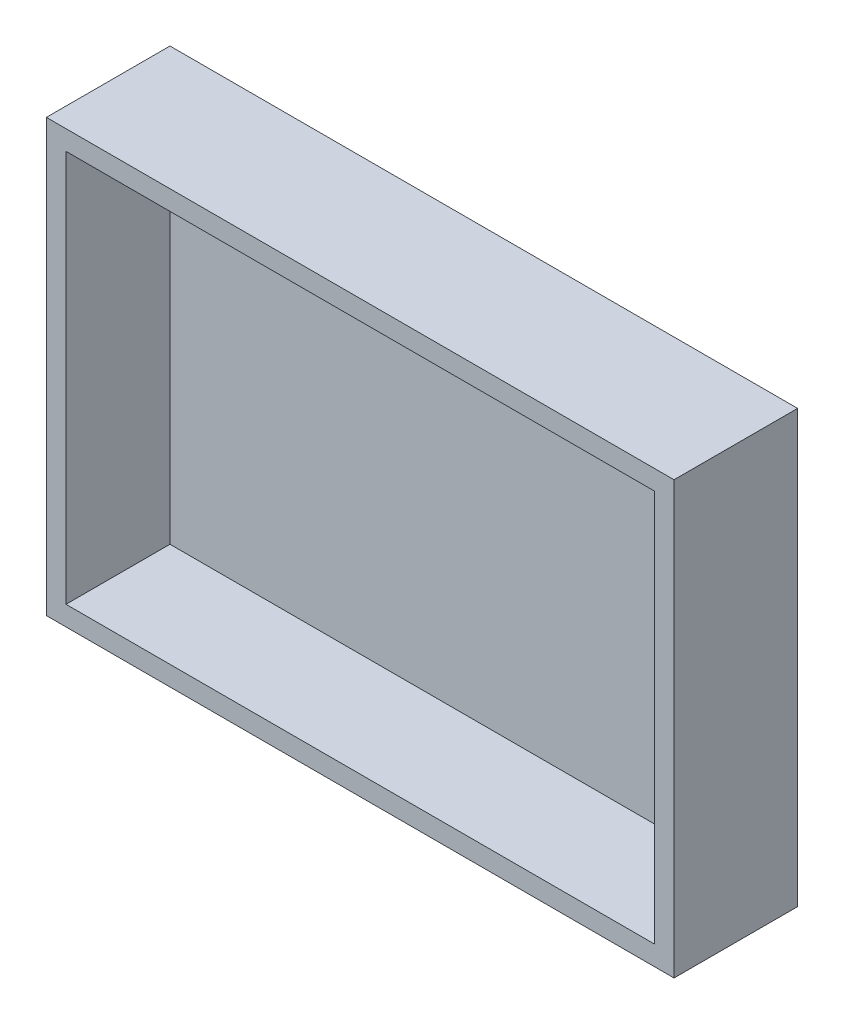
SolidWorks part; units mm, degrees
ref_plane "Front Plane" through (0, 0, 0) normal (0, 0, 1) x (1, 0, 0)
ref_plane "Top Plane" through (0, 0, 0) normal (0, 1, 0) x (1, 0, 0)
ref_plane "Right Plane" through (0, 0, 0) normal (1, 0, 0) x (0, 0, -1)
sketch "Sketch1" plane through (0, 0, 0) normal (0, 0, 1) x (1, 0, 0)
  line L1 (75, -50) -> (-75, -50)
  line L2 (75, -50) -> (75, 50)
  line L3 (75, 50) -> (-75, 50)
  line L4 (-75, -50) -> (-75, 50)
  line L5 (75, -50) -> (-75, 50) construction
  line L6 (75, 50) -> (-75, -50) construction
  point P0 (0, 0)
  dimension "D1" = 150
  dimension "D2" = 100
extrude "Boss-Extrude1" add sketch "Sketch1" along normal blind 5
sketch "Sketch2" plane through (0, -50, 0) normal (0, -1, 0) x (1, 0, 0)
  line L1 (-75, 0) -> (75, 0)
  line L2 (-75, 0) -> (-75, 31.5068)
  line L3 (-75, 31.5068) -> (75, 31.5068)
  line L4 (75, 0) -> (75, 31.5068)
extrude "Boss-Extrude2" add sketch "Sketch2" along normal blind 5
sketch "Sketch4" plane through (75, 0, 0) normal (1, 0, 0) x (0, 0, -1)
  line L1 (0, 50) -> (-31.5068, 50)
  line L2 (0, 50) -> (0, -55)
  line L3 (0, -55) -> (-31.5068, -55)
  line L4 (-31.5068, 50) -> (-31.5068, -55)
extrude "Boss-Extrude3" add sketch "Sketch4" along normal blind 5
sketch "Sketch5" plane through (0, 50, 0) normal (0, 1, 0) x (1, 0, 0)
  line L1 (-75, 0) -> (80, 0)
  line L2 (-75, 0) -> (-75, -31.5068)
  line L3 (-75, -31.5068) -> (80, -31.5068)
  line L4 (80, 0) -> (80, -31.5068)
extrude "Boss-Extrude4" add sketch "Sketch5" along normal blind 5
sketch "Sketch6" plane through (-75, 0, 0) normal (-1, 0, 0) x (0, 0, 1)
  line L1 (0, 55) -> (31.5068, 55)
  line L2 (0, 55) -> (0, -55)
  line L3 (0, -55) -> (31.5068, -55)
  line L4 (31.5068, 55) -> (31.5068, -55)
extrude "Boss-Extrude5" add sketch "Sketch6" along normal blind 5
